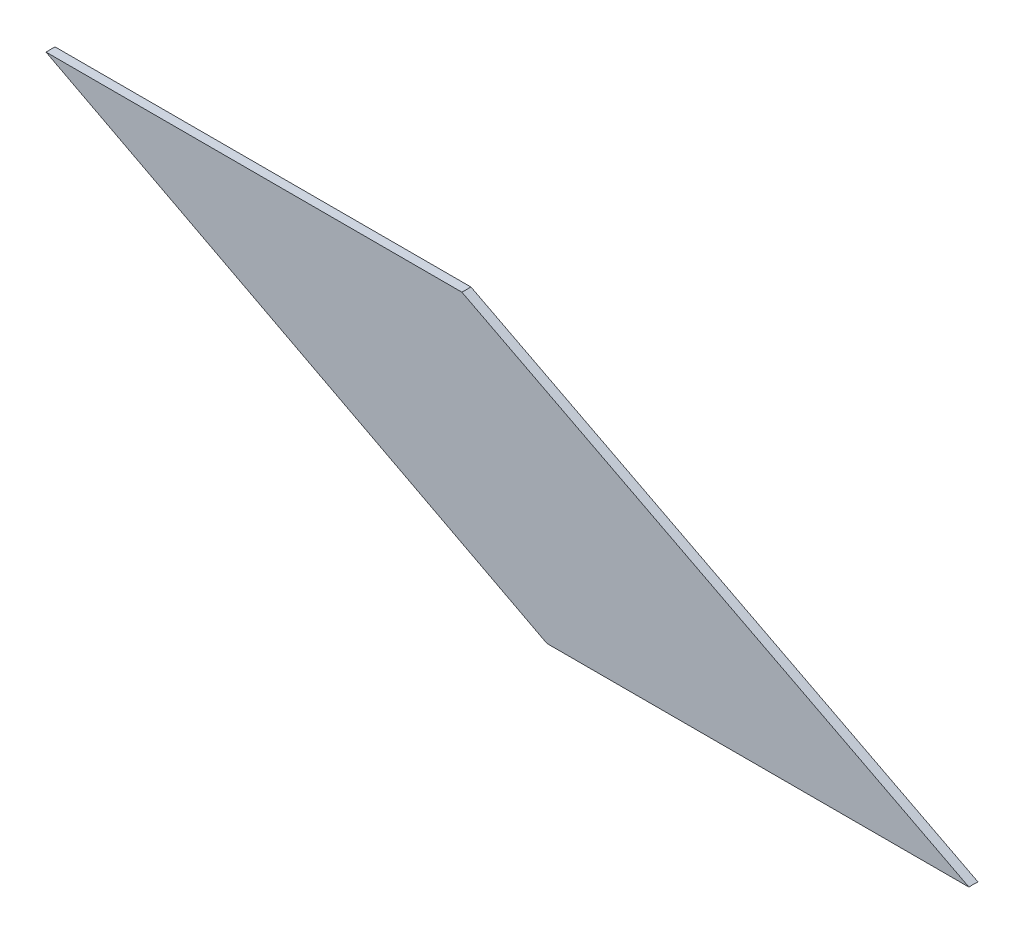
SolidWorks part; units mm, degrees
ref_plane "Front Plane" through (0, 0, 0) normal (0, 0, 1) x (1, 0, 0)
ref_plane "Top Plane" through (0, 0, 0) normal (0, 1, 0) x (1, 0, 0)
ref_plane "Right Plane" through (0, 0, 0) normal (1, 0, 0) x (0, 0, -1)
sketch "Sketch1" plane through (0, 0, 0) normal (0, 0, 1) x (1, 0, 0)
  line L0 (-4871.8981, 14.5) -> (-4929.322, 44.5)
  line L1 (-4929.322, 44.5) -> (-4883.222, 44.5)
  line L2 (-4883.222, 44.5) -> (-4825.0981, 14.5)
  line L3 (-4825.0981, 14.5) -> (-4871.8981, 14.5)
  point P2 (0, 0)
  point P3 (-786.3287, 24.5059)
  point P6 (-742.3029, 27.9436)
  point P8 (-907.1141, 14.55)
  point P10 (0, 0)
  point P13 (-870.5331, 63.5801)
  point P14 (-946.7649, 44.5)
  dimension "D1" = 46.8
  dimension "D2" = 46.1
  dimension "D3" = 14.5
  dimension "D4" = 30
  dimension "D5" = 27.3
extrude "Boss-Extrude1" add sketch "Sketch1" along normal mid plane 1
sketch "Sketch5" plane through (0, 0, 0) normal (1, 0, 0) x (0, 0, -1)
  circle A0 centre (0, 0) radius 15.5
extrude "Cut-Extrude1" cut sketch "Sketch5" against normal through all both and the other way through all
